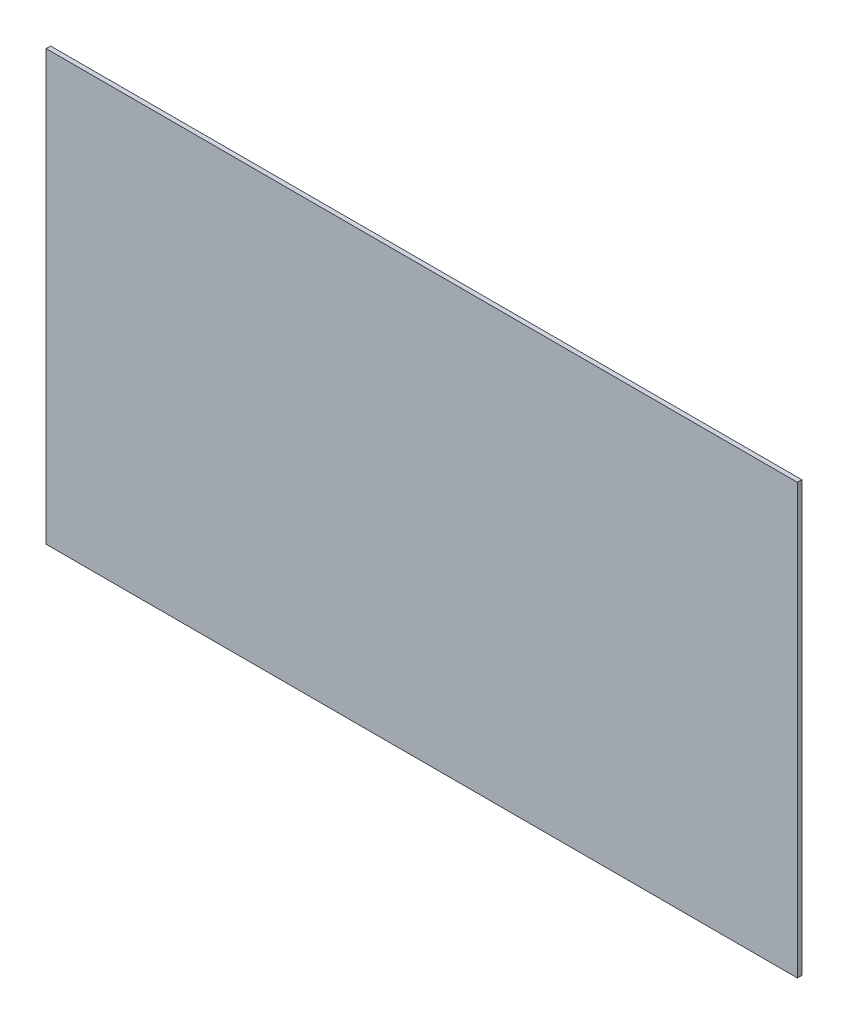
SolidWorks part; units mm, degrees
ref_plane "Front Plane" through (0, 0, 0) normal (0, 0, 1) x (1, 0, 0)
ref_plane "Top Plane" through (0, 0, 0) normal (0, 1, 0) x (1, 0, 0)
ref_plane "Right Plane" through (0, 0, 0) normal (1, 0, 0) x (0, 0, -1)
sketch "Sketch1" plane through (0, 0, 0) normal (0, 0, 1) x (1, 0, 0)
  line L0 (0, 0) -> (-1066.8, 0)
  line L1 (-1066.8, 0) -> (-1066.8, 609.6)
  line L2 (-1066.8, 609.6) -> (0, 609.6)
  line L3 (0, 609.6) -> (0, 0)
  dimension "D1" = 1066.8
  dimension "D2" = 609.6
extrude "Boss-Extrude1" add sketch "Sketch1" along normal blind 6.35
